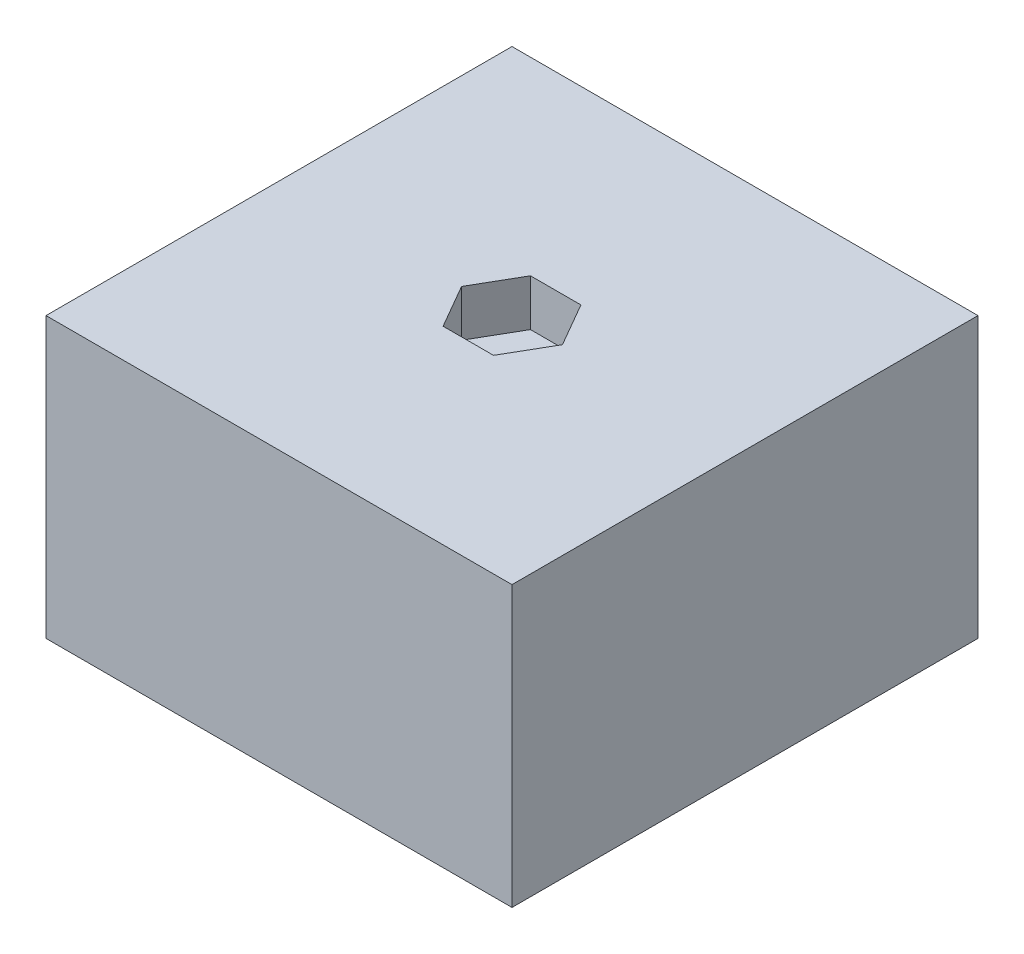
SolidWorks part; units mm, degrees
ref_plane "Front Plane" through (0, 0, 0) normal (0, 0, 1) x (1, 0, 0)
ref_plane "Top Plane" through (0, 0, 0) normal (0, 1, 0) x (1, 0, 0)
ref_plane "Right Plane" through (0, 0, 0) normal (1, 0, 0) x (0, 0, -1)
sketch "Sketch1" plane through (0, 0, 0) normal (0, 1, 0) x (1, 0, 0)
  line L1 (-6.35, 6.35) -> (6.35, 6.35)
  line L2 (-6.35, 6.35) -> (-6.35, -6.35)
  line L3 (-6.35, -6.35) -> (6.35, -6.35)
  line L4 (6.35, 6.35) -> (6.35, -6.35)
  line L5 (-6.35, 6.35) -> (6.35, -6.35) construction
  line L6 (-6.35, -6.35) -> (6.35, 6.35) construction
  point P0 (0, 0)
  dimension "D1" = 12.7
  dimension "D2" = 12.7
extrude "Boss-Extrude1" add sketch "Sketch1" along normal blind 7.62
sketch "Sketch2" plane through (0, 7.62, 0) normal (0, 1, 0) x (1, 0, 0)
  line L1 (0.6874, -1.1906) -> (1.3748, 0)
  line L2 (1.3748, 0) -> (0.6874, 1.1906)
  line L3 (0.6874, 1.1906) -> (-0.6874, 1.1906)
  line L4 (-0.6874, 1.1906) -> (-1.3748, 0)
  line L5 (-1.3748, 0) -> (-0.6874, -1.1906)
  line L6 (-0.6874, -1.1906) -> (0.6874, -1.1906)
  circle A0 centre (0, 0) radius 1.1906 construction
  dimension "D1" = 2.3813
extrude "Cut-Extrude1" cut sketch "Sketch2" against normal blind 1.27
